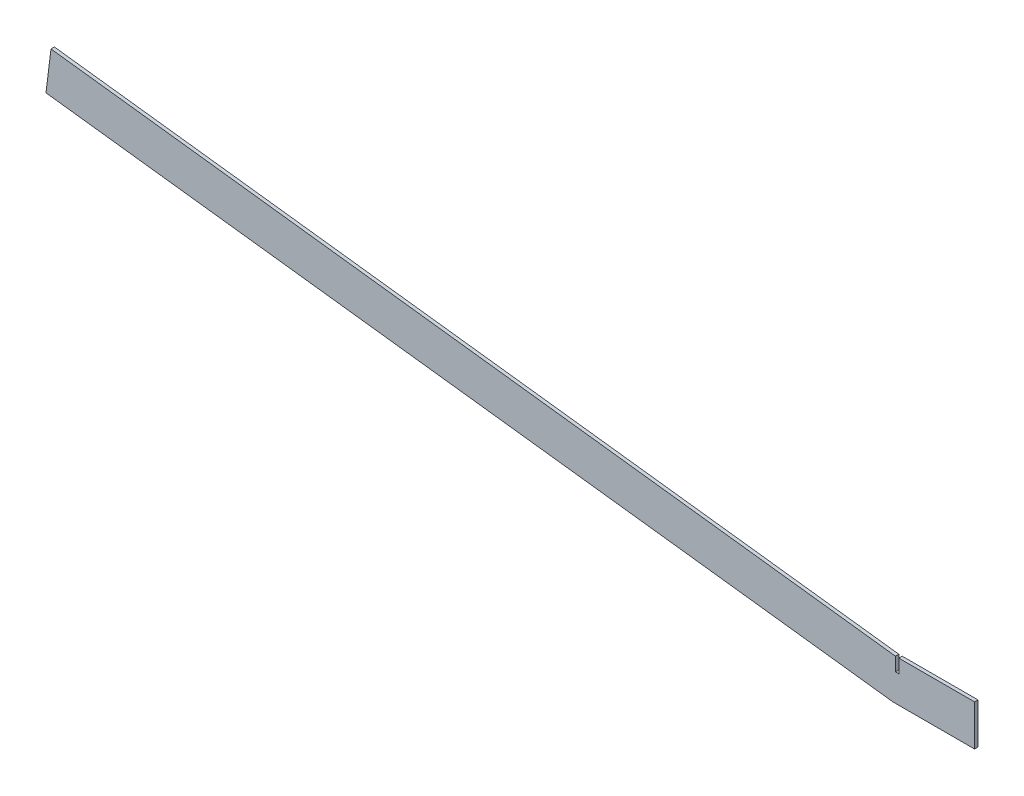
SolidWorks part; units mm, degrees
ref_plane "Front Plane" through (0, 0, 0) normal (0, 0, 1) x (1, 0, 0)
ref_plane "Top Plane" through (0, 0, 0) normal (0, 1, 0) x (1, 0, 0)
ref_plane "Right Plane" through (0, 0, 0) normal (1, 0, 0) x (0, 0, -1)
sketch "Sketch1" plane through (0, 0, 0) normal (0, 0, 1) x (1, 0, 0)
  line L0 (0, 0) -> (-789.745, 96.9685)
  line L1 (-789.745, 96.9685) -> (-785.1018, 134.7845)
  line L2 (-785.1018, 134.7845) -> (2.3303, 38.1)
  line L3 (2.3303, 38.1) -> (76.2, 38.1)
  line L4 (76.2, 38.1) -> (76.2, 0)
  line L5 (76.2, 0) -> (0, 0)
  line L6 (2.3303, 38.1) -> (2.3303, 25.4)
  line L7 (2.3303, 25.4) -> (5.5053, 25.4)
  line L8 (5.5053, 25.4) -> (5.5053, 38.1)
  dimension "D1" = 795.6759
  dimension "D2" = 38.1
  dimension "D3" = 38.1
  dimension "D4" = 3.175
  dimension "D5" = 12.7
  dimension "D6" = 7
  dimension "D7" = 76.2
extrude "Boss-Extrude1" add sketch "Sketch1" along normal mid plane 3.175 contours L8 L7 L6 L2 L1 L0 L5 L4 L3
